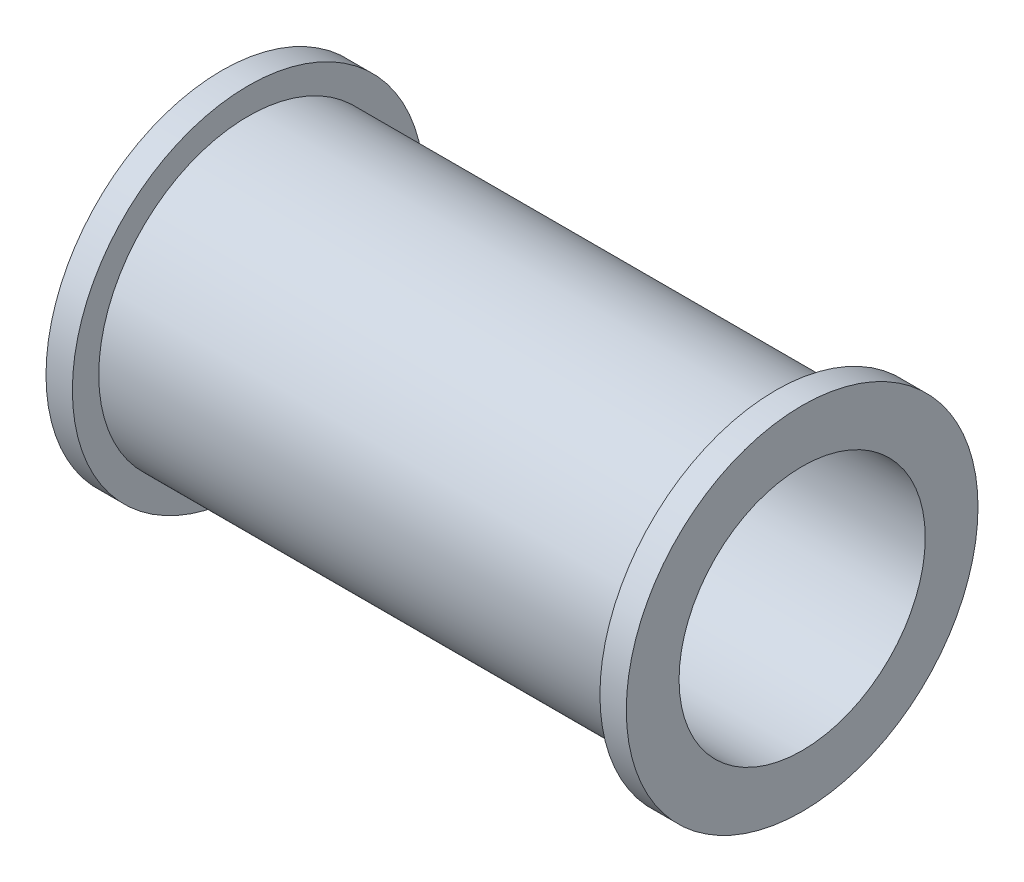
SolidWorks part; units mm, degrees
material "Резина"
ref_plane "Спереди" through (0, 0, 0) normal (0, 0, 1) x (1, 0, 0)
ref_plane "Сверху" through (0, 0, 0) normal (0, 1, 0) x (1, 0, 0)
ref_plane "Справа" through (0, 0, 0) normal (1, 0, 0) x (0, 0, -1)
sketch "Эскиз2" plane through (0, 0, 0) normal (0, 1, 0) x (1, 0, 0)
  line L0 (0, 0) -> (0, 10)
  line L1 (0, 10) -> (1.5, 10)
  line L2 (1.5, 10) -> (1.5, 8.5)
  line L3 (1.5, 8.5) -> (31.5, 8.5)
  line L4 (33, 0) -> (0, 0)
  line L5 (16.5, 8.5) -> (16.5, 0) construction
  line L6 (33, 0) -> (33, 10)
  line L7 (33, 10) -> (31.5, 10)
  line L8 (31.5, 10) -> (31.5, 8.5)
  dimension "D1" = 1.5
  dimension "D2" = 8.5
  dimension "D3" = 10
  dimension "D4" = 15
revolve "Повернуть1" add sketch "Эскиз2" angle 360 about L4
sketch "Эскиз3" plane through (33, 0, 0) normal (1, 0, 0) x (0, 0, -1)
  circle A0 centre (0, 0) radius 7
  dimension "D1" = 14
extrude "Вырез-Вытянуть1" cut sketch "Эскиз3" against normal through all
equation "\"D3@Эскиз2\"=\"D2@Эскиз2\"+1.5"
